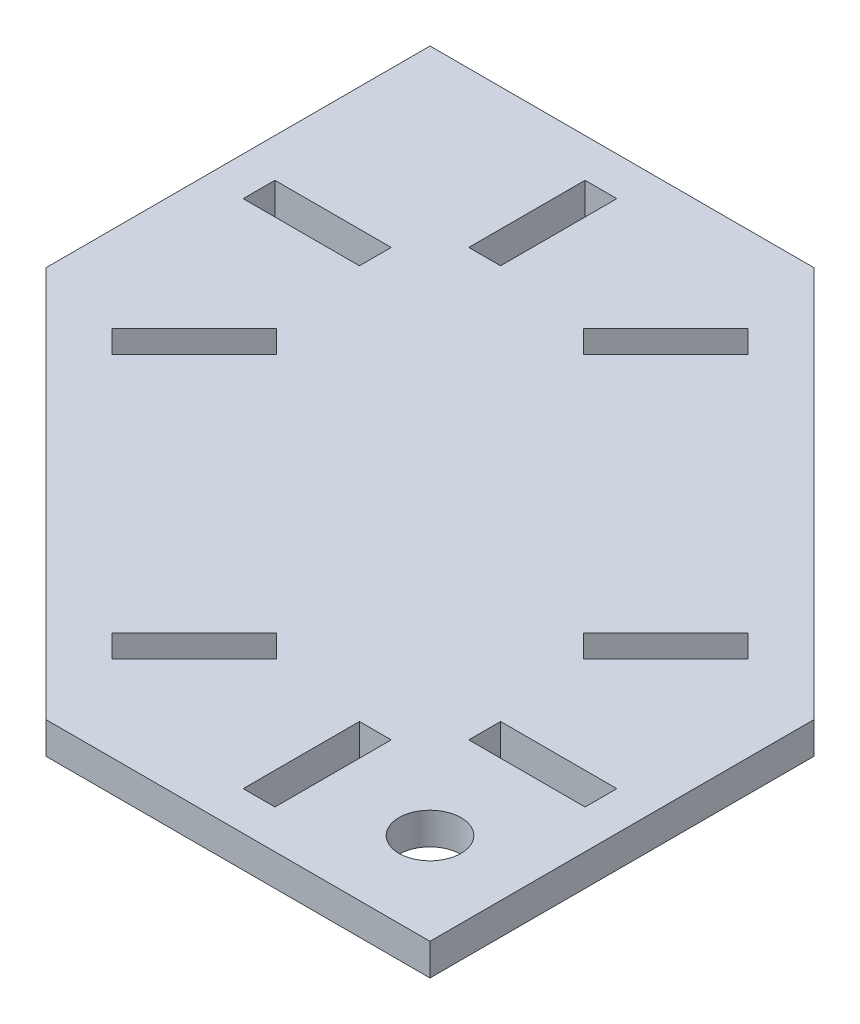
SolidWorks part; units mm, degrees
material "Corrugated Paper"
ref_plane "Front Plane" through (0, 0, 0) normal (0, 0, 1) x (1, 0, 0)
ref_plane "Top Plane" through (0, 0, 0) normal (0, 1, 0) x (1, 0, 0)
ref_plane "Right Plane" through (0, 0, 0) normal (1, 0, 0) x (0, 0, -1)
sketch "Sketch1" plane through (0, 0, 0) normal (0, 1, 0) x (1, 0, 0)
  line L0 (-20.9, 30) -> (-25, 30)
  line L1 (-50, -50) -> (50, -50)
  line L2 (-50, -50) -> (-50, 50)
  line L3 (-50, 50) -> (50, 50)
  line L4 (50, -50) -> (50, 50)
  line L5 (-50, -50) -> (50, 50) construction
  line L6 (-50, 50) -> (50, -50) construction
  line L7 (-30, 30) -> (30, 30) construction
  line L8 (-30, 30) -> (-30, -30) construction
  line L9 (-30, -30) -> (30, -30) construction
  line L10 (30, 30) -> (30, -30) construction
  line L11 (-30, 20.9) -> (-45, 20.9)
  line L12 (-30, 20.9) -> (-30, 25)
  line L13 (-30, 25) -> (-45, 25)
  line L14 (-45, 20.9) -> (-45, 25)
  line L15 (-25, 30) -> (-25, 45)
  line L16 (-20.9, 45) -> (-25, 45)
  line L17 (-20.9, 30) -> (-20.9, 45)
  line L18 (30, -20.9) -> (30, -25)
  line L19 (45, -20.9) -> (45, -25)
  line L20 (30, -25) -> (45, -25)
  line L21 (30, -20.9) -> (45, -20.9)
  line L22 (20.9, -30) -> (25, -30)
  line L23 (25, -30) -> (25, -45)
  line L24 (20.9, -45) -> (25, -45)
  line L25 (20.9, -30) -> (20.9, -45)
  line L26 (0, -50) -> (0, 50) construction
  line L27 (50, 0) -> (-50, 0) construction
  line L28 (45, 20.9) -> (45, 25)
  line L29 (30, 25) -> (45, 25)
  line L30 (30, 20.9) -> (30, 25)
  line L31 (30, 20.9) -> (45, 20.9)
  line L32 (-30, -20.9) -> (-30, -25)
  line L33 (-45, -20.9) -> (-45, -25)
  line L34 (-30, -25) -> (-45, -25)
  line L35 (-30, -20.9) -> (-45, -20.9)
  line L36 (20.9, 45) -> (25, 45)
  line L37 (25, 30) -> (25, 45)
  line L38 (20.9, 30) -> (25, 30)
  line L39 (20.9, 30) -> (20.9, 45)
  line L40 (-20.9, -30) -> (-25, -30)
  line L41 (-20.9, -45) -> (-25, -45)
  line L42 (-20.9, -30) -> (-20.9, -45)
  line L43 (-25, -30) -> (-25, -45)
  circle A0 centre (38.1838, -38.1838) radius 4
  point P47 (0, 0)
  point P48 (0, 0)
  point P50 (0, 0)
  dimension "D3" = 8
  dimension "D1" = 100
  dimension "D2" = 100
  dimension "D4" = 15
  dimension "D5" = 4.1
  dimension "D6" = 50
  dimension "D7" = 60
extrude "Boss-Extrude1" add sketch "Sketch1" along normal blind 4.1
ref_plane "Plane1" through (0, 0, 0) normal (-0.7071, 0, 0.7071) x (0.7071, 0, 0.7071)
sketch "Sketch2" plane through (0, 0, 0) normal (-0.7071, 0, 0.7071) x (0.7071, 0, 0.7071)
  line L1 (70.7107, 4.1) -> (-70.7107, 4.1)
  line L2 (70.7107, 4.1) -> (70.7107, 0)
  line L3 (70.7107, 0) -> (-70.7107, 0)
  line L4 (-70.7107, 4.1) -> (-70.7107, 0)
extrude "Cut-Extrude1" cut sketch "Sketch2" along normal up to vertex from offset 35
sketch "Sketch3" plane through (0, 0, 0) normal (-0.7071, 0, 0.7071) x (0.7071, 0, 0.7071)
  line L0 (0, 0) -> (-70.7107, 0) construction
  line L1 (70.7107, 4.1) -> (-70.7107, 4.1)
  line L2 (70.7107, 4.1) -> (70.7107, 0)
  line L3 (70.7107, 0) -> (-70.7107, 0)
  line L4 (-70.7107, 4.1) -> (-70.7107, 0)
  line L5 (-70.7107, 4.1) -> (-70.7107, 0) construction
extrude "Cut-Extrude2" cut sketch "Sketch3" against normal up to next from offset 35 offset against normal yes
sketch "Sketch4" plane through (0, 4.1, 0) normal (0, 1, 0) x (1, 0, 0)
  line L0 (-38.9616, -2.0506) -> (-36.0624, -4.9497)
  line L1 (-36.0624, -4.9497) -> (-25.4558, 5.6569)
  line L2 (-25.4558, 5.6569) -> (-28.355, 8.556)
  line L3 (-28.355, 8.556) -> (-38.9616, -2.0506)
  line L5 (-45, 20.9) -> (-30, 20.9) construction
  line L6 (-6.4903, 6.4903) -> (6.4903, -6.4903) construction
  line L7 (-24.7487, -24.7487) -> (24.7487, 24.7487) construction
  line L8 (0.5025, -50) -> (-50, 0.5025) construction
  line L9 (50, -0.5025) -> (-0.5025, 50) construction
  line L10 (8.556, -28.355) -> (-2.0506, -38.9616)
  line L11 (5.6569, -25.4558) -> (8.556, -28.355)
  line L12 (-4.9497, -36.0624) -> (5.6569, -25.4558)
  line L13 (-2.0506, -38.9616) -> (-4.9497, -36.0624)
  line L14 (-50, 50) -> (50, -50) construction
  line L15 (38.9616, 2.0506) -> (36.0624, 4.9497)
  line L16 (36.0624, 4.9497) -> (25.4558, -5.6569)
  line L17 (25.4558, -5.6569) -> (28.355, -8.556)
  line L18 (28.355, -8.556) -> (38.9616, 2.0506)
  line L19 (-8.556, 28.355) -> (2.0506, 38.9616)
  line L20 (-5.6569, 25.4558) -> (-8.556, 28.355)
  line L21 (4.9497, 36.0624) -> (-5.6569, 25.4558)
  line L22 (2.0506, 38.9616) -> (4.9497, 36.0624)
  line L23 (-30, 20.9) -> (-30, 25) construction
  dimension "D1" = 14
  dimension "D2" = 22
extrude "Cut-Extrude3" cut sketch "Sketch4" against normal through all
